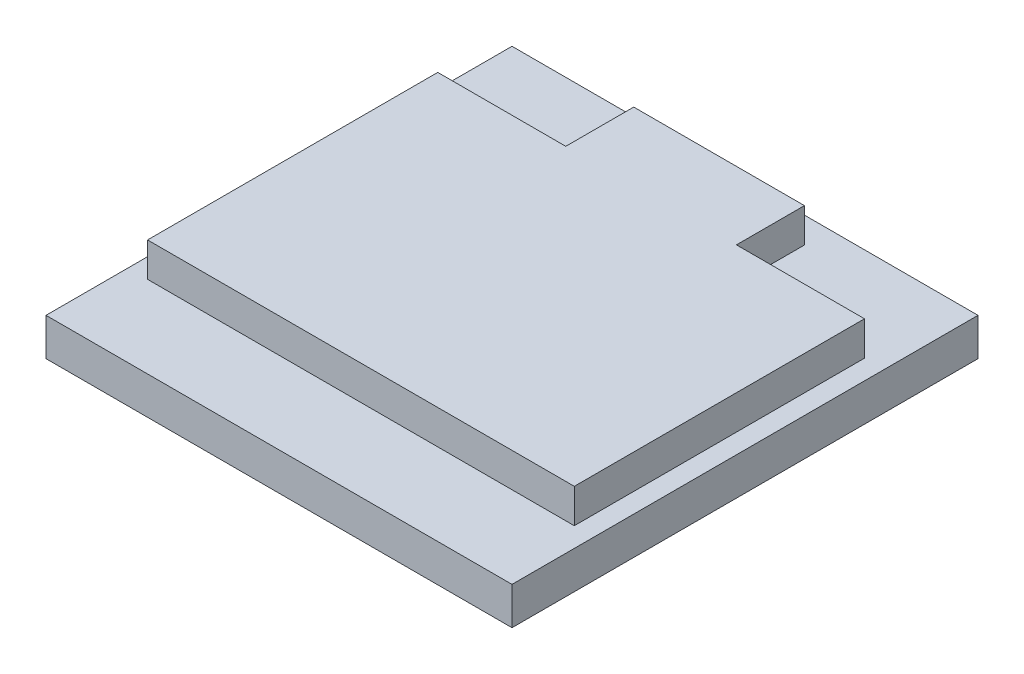
SolidWorks part; units mm, degrees
ref_plane "Front Plane" through (0, 0, 0) normal (0, 0, 1) x (1, 0, 0)
ref_plane "Top Plane" through (0, 0, 0) normal (0, 1, 0) x (1, 0, 0)
ref_plane "Right Plane" through (0, 0, 0) normal (1, 0, 0) x (0, 0, -1)
sketch "Sketch1" plane through (0, 0, 0) normal (0, 1, 0) x (1, 0, 0)
  line L1 (-13.65, -13.65) -> (13.65, -13.65)
  line L2 (-13.65, -13.65) -> (-13.65, 13.65)
  line L3 (-13.65, 13.65) -> (13.65, 13.65)
  line L4 (13.65, -13.65) -> (13.65, 13.65)
  line L5 (-13.65, -13.65) -> (13.65, 13.65) construction
  line L6 (-13.65, 13.65) -> (13.65, -13.65) construction
  point P0 (0, 0)
  dimension "D1" = 27.3
  dimension "D2" = 27.3
extrude "Boss-Extrude1" add sketch "Sketch1" along normal blind 2.2
sketch "Sketch2" plane through (0, 2.2, 0) normal (0, 1, 0) x (1, 0, 0)
  line L0 (13.65, 13.65) -> (-13.65, 13.65) construction
  line L1 (-12.5, -8.85) -> (12.5, -8.85)
  line L2 (-12.5, -8.85) -> (-12.5, 8.15)
  line L3 (-12.5, 8.15) -> (12.5, 8.15)
  line L4 (12.5, -8.85) -> (12.5, 8.15)
  line L5 (-12.5, -8.85) -> (12.5, 8.15) construction
  line L6 (-12.5, 8.15) -> (12.5, -8.85) construction
  line L8 (-5, 4.1679) -> (5, 4.1679)
  line L9 (-5, 4.1679) -> (-5, 12.1321)
  line L10 (-5, 12.1321) -> (5, 12.1321)
  line L11 (5, 4.1679) -> (5, 12.1321)
  line L12 (-5, 4.1679) -> (5, 12.1321) construction
  line L13 (-5, 12.1321) -> (5, 4.1679) construction
  point P0 (0, -0.35)
  point P8 (0, 8.15)
  dimension "D1" = 25
  dimension "D2" = 17
  dimension "D3" = 5.5
  dimension "D4" = 10
extrude "Boss-Extrude3" add sketch "Sketch2" along normal blind 2 contours L3 L11 L10 L9 | L11 L8 L9 L3 L2 L1 L4 | L8 L11 L3 L9
